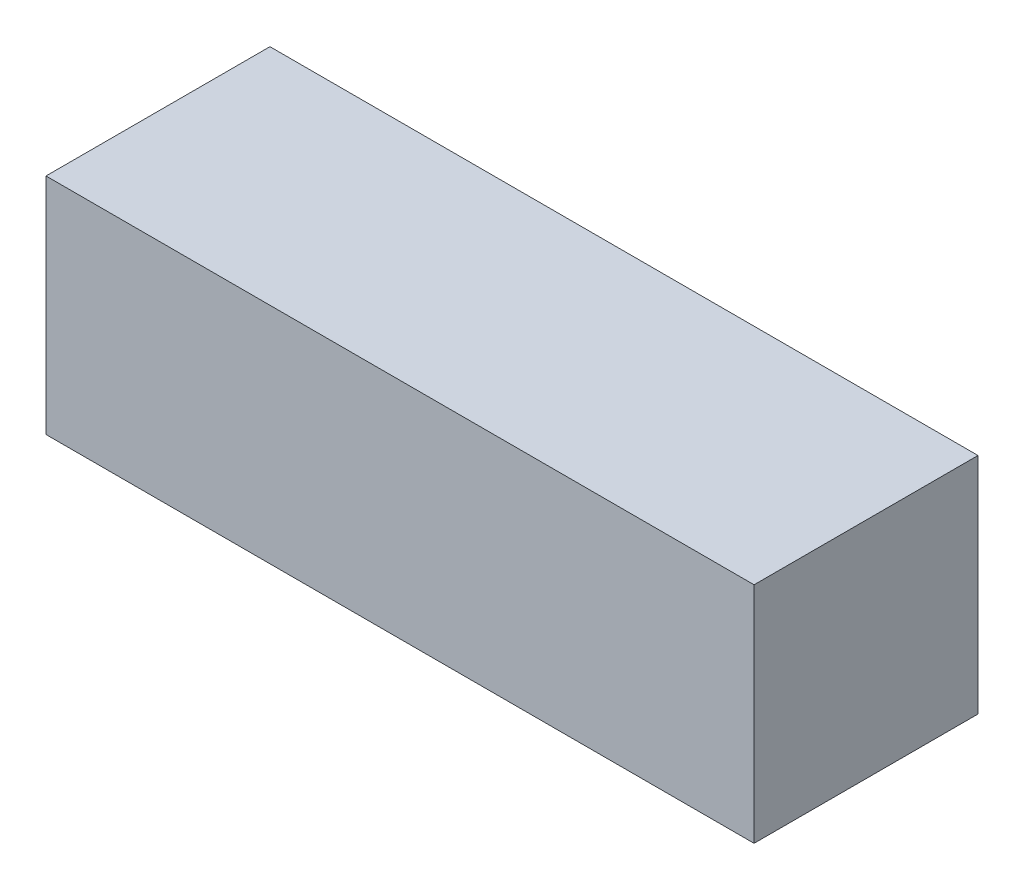
SolidWorks part; units mm, degrees
material "Berillio"
ref_plane "Piano frontale" through (0, 0, 0) normal (0, 0, 1) x (1, 0, 0)
ref_plane "Piano superiore" through (0, 0, 0) normal (0, 1, 0) x (1, 0, 0)
ref_plane "Piano destro" through (0, 0, 0) normal (1, 0, 0) x (0, 0, -1)
sketch "Schizzo1" plane through (0, 0, 0) normal (0, 1, 0) x (1, 0, 0)
  line L1 (-80, 25.3) -> (80, 25.3)
  line L2 (-80, 25.3) -> (-80, -25.3)
  line L3 (-80, -25.3) -> (80, -25.3)
  line L4 (80, 25.3) -> (80, -25.3)
  line L5 (-80, 25.3) -> (80, -25.3) construction
  line L6 (-80, -25.3) -> (80, 25.3) construction
  point P0 (0, 0)
  dimension "D1" = 160
  dimension "D2" = 50.6
extrude "Estrusione-Estrusione1" add sketch "Schizzo1" along normal blind 50.6
